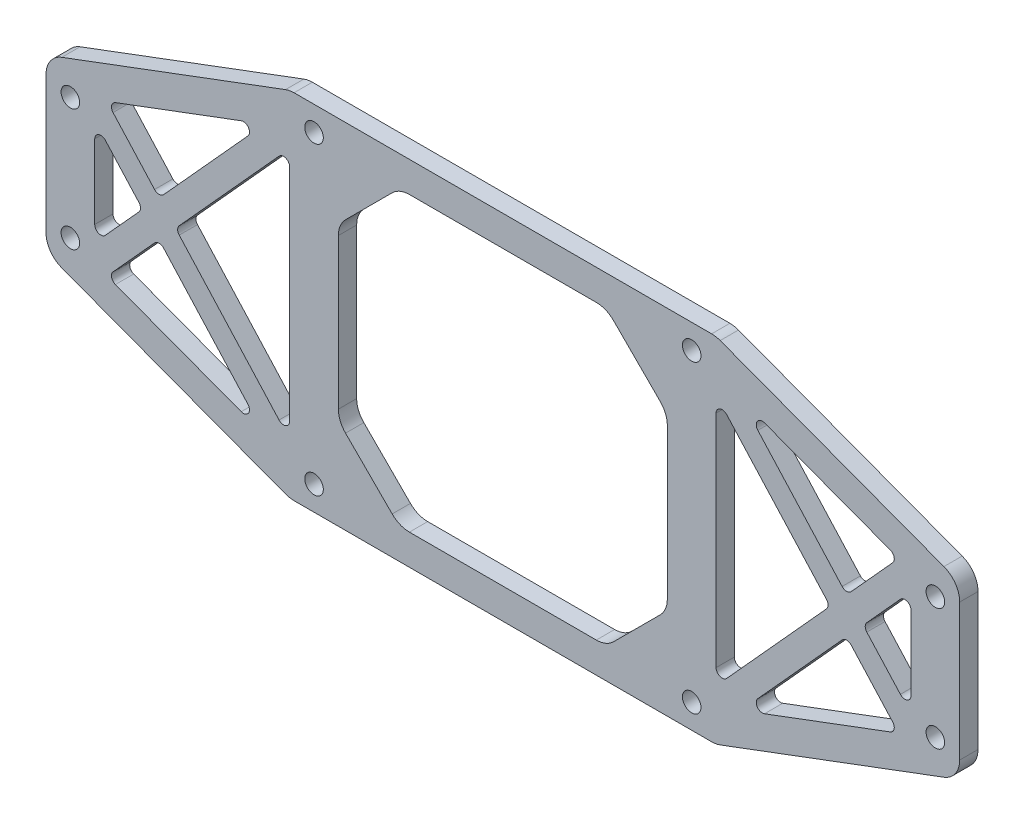
SolidWorks part; units mm, degrees
material "Thornel Mat VMA"
ref_plane "前视基准面" through (0, 0, 0) normal (0, 0, 1) x (1, 0, 0)
ref_plane "上视基准面" through (0, 0, 0) normal (0, 1, 0) x (1, 0, 0)
ref_plane "右视基准面" through (0, 0, 0) normal (1, 0, 0) x (0, 0, -1)
other "Configuration Table"
sketch "草图1" plane through (0, 0, 0) normal (0, 0, 1) x (1, 0, 0)
  line L0 (-75, 14) -> (-35, 29)
  line L1 (-31, -25) -> (31, -25) construction
  line L2 (-31, -25) -> (-31, 25) construction
  line L3 (-31, 25) -> (31, 25) construction
  line L4 (31, -25) -> (31, 25) construction
  line L5 (-31, -25) -> (31, 25) construction
  line L6 (-31, 25) -> (31, -25) construction
  line L7 (-71, -10) -> (71, -10) construction
  line L8 (-71, -10) -> (-71, 10) construction
  line L9 (-71, 10) -> (71, 10) construction
  line L10 (71, -10) -> (71, 10) construction
  line L11 (-71, -10) -> (71, 10) construction
  line L12 (-71, 10) -> (71, -10) construction
  line L13 (35, -29) -> (-35, -29)
  line L14 (35, -29) -> (35, 29)
  line L15 (35, 29) -> (-35, 29)
  line L16 (-35, -29) -> (-35, 29)
  line L17 (35, -29) -> (-35, 29) construction
  line L18 (35, 29) -> (-35, -29) construction
  line L19 (75, -14) -> (-75, -14)
  line L20 (75, -14) -> (75, 14)
  line L21 (75, 14) -> (-75, 14)
  line L22 (-75, -14) -> (-75, 14)
  line L23 (75, -14) -> (-75, 14) construction
  line L24 (75, 14) -> (-75, -14) construction
  line L25 (35, 29) -> (75, 14)
  line L26 (-75, -14) -> (-35, -29)
  line L27 (35, -29) -> (75, -14)
  circle A0 centre (-71, 10) radius 1.525
  circle A1 centre (-71, -10) radius 1.525
  circle A2 centre (71, 10) radius 1.525
  circle A3 centre (71, -10) radius 1.525
  circle A4 centre (-31, 25) radius 1.525
  circle A5 centre (31, 25) radius 1.525
  circle A6 centre (31, -25) radius 1.525
  circle A7 centre (-31, -25) radius 1.525
  point P0 (0, 0)
  point P6 (0, 0)
  point P19 (0, 0)
  point P24 (0, 0)
  dimension "D5" = 3.05
  dimension "D1" = 50
  dimension "D2" = 62
  dimension "D3" = 142
  dimension "D4" = 20
  dimension "D6" = 4
  dimension "D7" = 4
  dimension "D8" = 4
  dimension "D9" = 4
extrude "凸台-拉伸1" add sketch "草图1" along normal blind 3 contours L21 L16 L0 | L22 L19 L16 L21 A1 A0 | L19 L26 L16 | L14 L19 L16 L13 A7 A6 | L14 L21 L16 L19 | L21 L14 L15 L16 A5 A4 | L25 L14 L21 | L20 L21 L14 L19 A3 A2 | L14 L27 L19
fillet "圆角1" radius 4 8 edges at (-35, 29, 1.5) (35, 29, 1.5) (75, 14, 1.5) (75, -14, 1.5) (35, -29, 1.5) (-35, -29, 1.5) (-75, -14, 1.5) (-75, 14, 1.5)
sketch "草图2" plane through (0, 0, 3) normal (0, 0, 1) x (1, 0, 0)
  line L0 (34.2747, 29) -> (-34.2747, 29) construction
  line L1 (27, -24) -> (-27, -24)
  line L2 (27, -24) -> (27, 24)
  line L3 (27, 24) -> (-27, 24)
  line L4 (-27, -24) -> (-27, 24)
  line L5 (27, -24) -> (-27, 24) construction
  line L6 (27, 24) -> (-27, -24) construction
  line L7 (-35, 23.66) -> (-67, 11.66)
  line L8 (-67, 11.66) -> (-67, -11.66)
  line L9 (-67, -11.66) -> (-35, -23.66)
  line L10 (-35, -23.66) -> (-35, 23.66)
  line L12 (-72.4045, 14.9733) -> (-35.6792, 28.7453) construction
  line L13 (-72.4045, -14.9733) -> (-35.6792, -28.7453) construction
  line L14 (0, 0) -> (0, -50000) construction
  line L19 (-67, 11.66) -> (-35, -23.66) construction
  line L20 (-67, -11.66) -> (-35, 23.66) construction
  line L21 (-68.4822, -10.3172) -> (-36.4822, 25.0028)
  line L22 (-65.5178, 13.0028) -> (-33.5178, -22.3172)
  line L23 (-65.5178, -13.0028) -> (-33.5178, 22.3172)
  line L24 (-68.4822, 10.3172) -> (-36.4822, -25.0028)
  line L25 (67, -11.66) -> (35, 23.66) construction
  line L26 (67, 11.66) -> (35, -23.66) construction
  line L27 (68.4822, 10.3172) -> (36.4822, -25.0028)
  line L28 (65.5178, -13.0028) -> (33.5178, 22.3172)
  line L29 (65.5178, 13.0028) -> (33.5178, -22.3172)
  line L30 (68.4822, -10.3172) -> (36.4822, 25.0028)
  line L31 (35, -23.66) -> (35, 23.66)
  line L32 (67, -11.66) -> (35, -23.66)
  line L33 (67, 11.66) -> (67, -11.66)
  line L34 (35, 23.66) -> (67, 11.66)
  circle A0 centre (-31, 25) radius 1.525 construction
  circle A1 centre (-71, 10) radius 1.525 construction
  point P0 (0, 0)
  dimension "D4" = 4
  dimension "D1" = 5
  dimension "D2" = 4
  dimension "D3" = 4
  dimension "D5" = 5
  dimension "D6" = 5
  dimension "D7" = 2
  dimension "D8" = 2
extrude "切除-拉伸1" cut sketch "草图2" against normal blind 3 contours L7 L22 L21 | L23 L22 L10 | L24 L23 L9 | L24 L8 L21 | L4 L1 L2 L3 | L31 L29 L28 | L34 L30 L29 | L33 L27 L30 | L32 L28 L27
chamfer "倒角1" distance 10 angle 45 4 edges at (-27, -24, 1.5) (27, -24, 1.5) (27, 24, 1.5) (-27, 24, 1.5)
fillet "圆角2" radius 4 8 edges at (27, 14, 1.5) (17, 24, 1.5) (-27, 14, 1.5) (-27, -14, 1.5) (-17, -24, 1.5) (17, -24, 1.5) (27, -14, 1.5) (-17, 24, 1.5)
fillet "圆角3" radius 1 24 edges at (64.9856, 12.4154, 1.5) (56.436, 2.9788, 1.5) (39.0875, 22.1272, 1.5) (39.0875, -22.1272, 1.5) (56.436, -2.9788, 1.5) (64.9856, -12.4154, 1.5) (-39.0875, -22.1272, 1.5) (-64.9856, -12.4154, 1.5) (-56.436, -2.9788, 1.5) (-59.1348, 0, 1.5) (-67, -8.6812, 1.5) (-67, 8.6812, 1.5) (-56.436, 2.9788, 1.5) (-64.9856, 12.4154, 1.5) (-39.0875, 22.1272, 1.5) (-35, 20.6812, 1.5) (-35, -20.6812, 1.5) (-53.7372, 0, 1.5) (67, -8.6812, 1.5) (59.1348, 0, 1.5) (67, 8.6812, 1.5) (53.7372, 0, 1.5) (35, -20.6812, 1.5) (35, 20.6812, 1.5)
